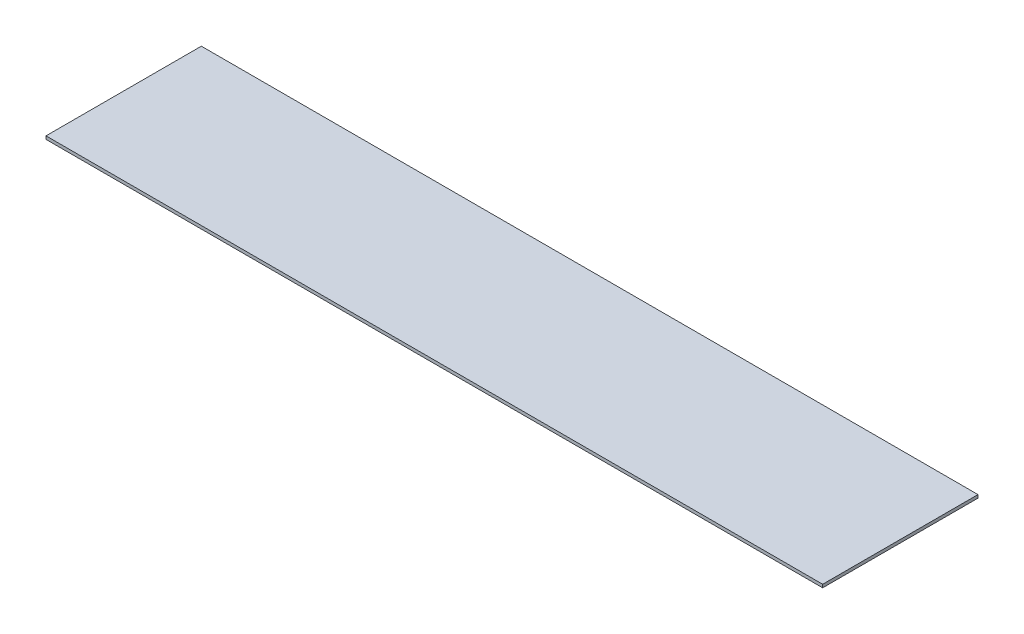
SolidWorks part; units mm, degrees
ref_plane "Ebene vorne" through (0, 0, 0) normal (0, 0, 1) x (1, 0, 0)
ref_plane "Ebene oben" through (0, 0, 0) normal (0, 1, 0) x (1, 0, 0)
ref_plane "Ebene rechts" through (0, 0, 0) normal (1, 0, 0) x (0, 0, -1)
sketch "Sketch1" plane through (0, 0, 0) normal (0, 1, 0) x (1, 0, 0)
  line L1 (-50, 10) -> (50, 10)
  line L2 (-50, 10) -> (-50, -10)
  line L3 (-50, -10) -> (50, -10)
  line L4 (50, 10) -> (50, -10)
  line L5 (-50, 10) -> (50, -10) construction
  line L6 (-50, -10) -> (50, 10) construction
  point P0 (0, 0)
  dimension "D1" = 100
  dimension "D2" = 20
extrude "Boss-Extrude1" add sketch "Sketch1" along normal blind 0.4
